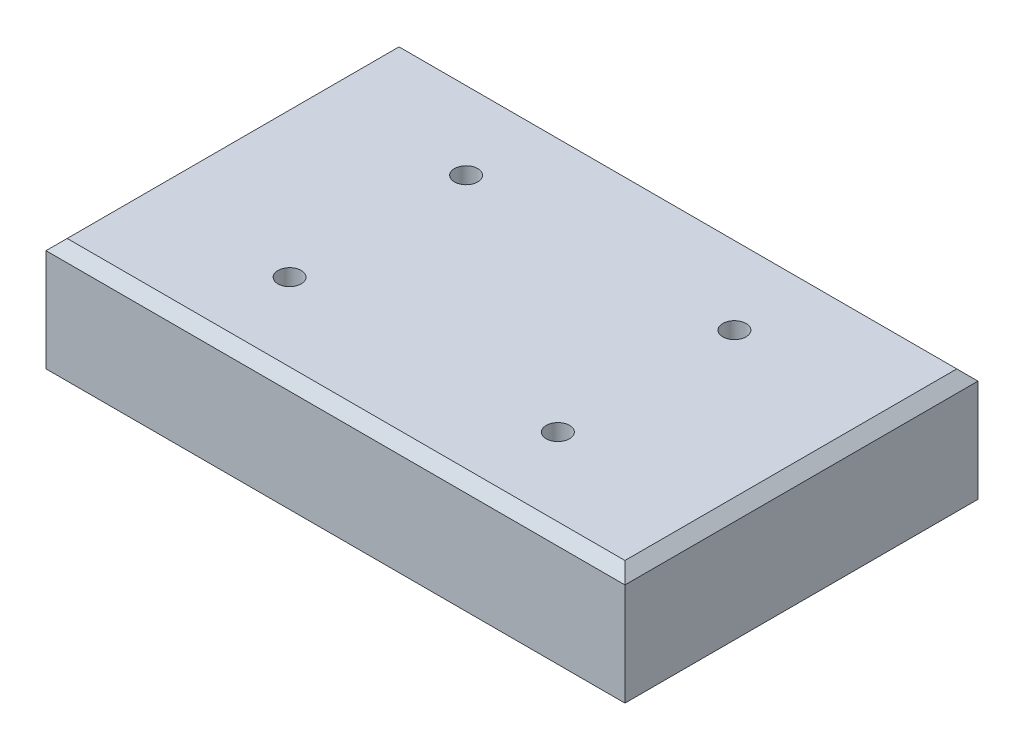
SolidWorks part; units mm, degrees
ref_plane "Front Plane" through (0, 0, 0) normal (0, 0, 1) x (1, 0, 0)
ref_plane "Top Plane" through (0, 0, 0) normal (0, 1, 0) x (1, 0, 0)
ref_plane "Right Plane" through (0, 0, 0) normal (1, 0, 0) x (0, 0, -1)
sketch "Sketch1" plane through (0, 0, 0) normal (0, 1, 0) x (1, 0, 0)
  line L1 (41, -25) -> (-41, -25)
  line L2 (41, -25) -> (41, 25)
  line L3 (41, 25) -> (-41, 25)
  line L4 (-41, -25) -> (-41, 25)
  line L5 (41, -25) -> (-41, 25) construction
  line L6 (41, 25) -> (-41, -25) construction
  point P0 (0, 0)
  dimension "D1" = 50
  dimension "D2" = 82
extrude "Boss-Extrude1" add sketch "Sketch1" along normal blind 16
chamfer "Chamfer1" distance 1.5 angle 45 4 edges at (-41, 16, 0) (0, 16, 25) (0, 16, -25) (41, 16, 0)
sketch "Sketch4" plane through (0, 16, 0) normal (0, 1, 0) x (1, 0, 0)
  line L0 (-41, 25) -> (41, 25) construction
  line L1 (41, 25) -> (41, -25) construction
  circle A0 centre (-19, 12.5) radius 3.762
  circle A1 centre (-19, -12.5) radius 9.4502
  circle A2 centre (19, -12.5) radius 10.9224
  circle A3 centre (19, 12.5) radius 3.0753
  point P12 (0, 0)
  point P13 (0, 0)
  point P14 (0, 0)
  point P15 (0, 0)
  dimension "D1" = 25
  dimension "D2" = 38
  dimension "D3" = 12.5
  dimension "D4" = 22
hole_wizard "M4 Tapped Hole1" positions "Sketch7" profile "Sketch8" tap size "M4" standard "ISO"
sketch "Sketch7" plane through (0, 16, 0) normal (0, 1, 0) x (1, 0, 0)
  point P0 (-19, 12.5)
  point P3 (19, 12.5)
  point P6 (19, -12.5)
  point P9 (-19, -12.5)
sketch "Sketch8" plane through (-19, 16, -12.5) normal (1, 0, 0) x (0, 0, 1)
  line L0 (0, 0) -> (0, 6.9914)
  line L1 (0, 6.9914) -> (1.65, 6)
  line L2 (1.65, 6) -> (1.65, 0)
  line L5 (1.65, 0) -> (0, 0)
  line L10 (0, 6.9914) -> (-1.65, 6) construction
  line L11 (0, -6.35) -> (0, 107.95) construction
  dimension "Tap Drill Dia." = 3.3
  dimension "Tap Drill Depth" = 6
  dimension "Drill Angle" = 118
